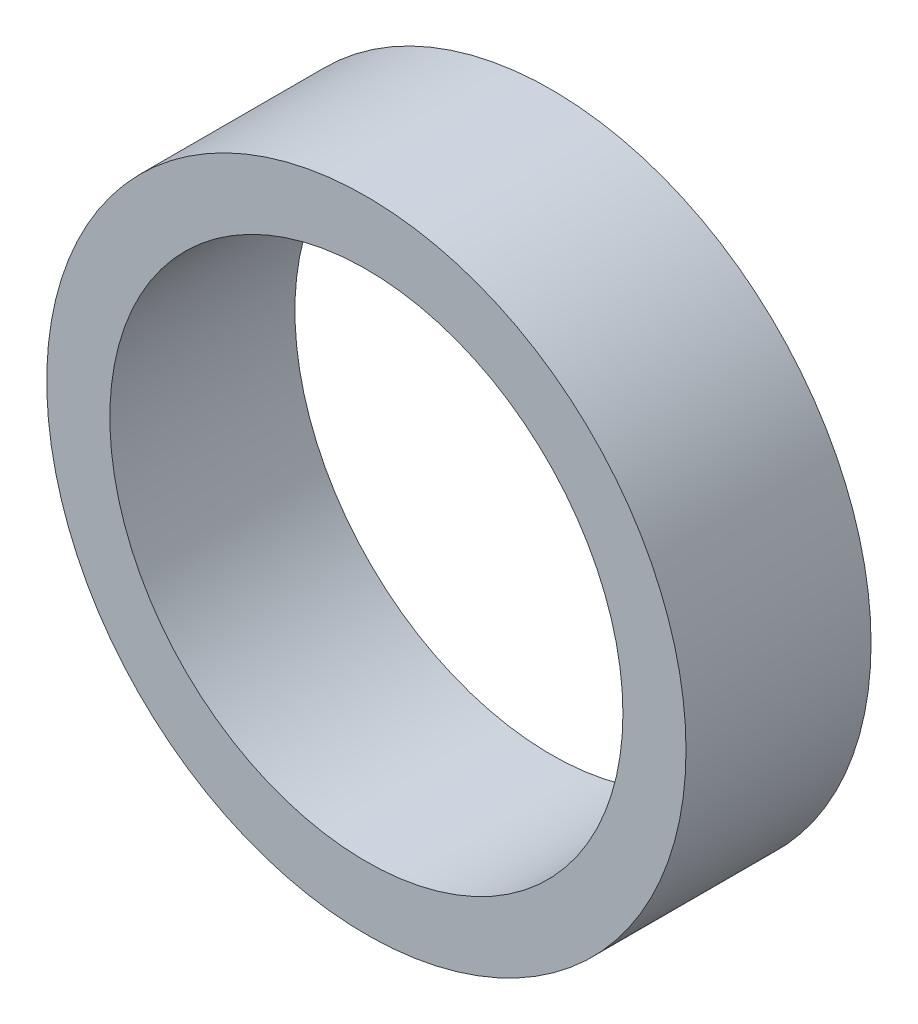
SolidWorks part; units mm, degrees
ref_plane "Front Plane" through (0, 0, 0) normal (0, 0, 1) x (1, 0, 0)
ref_plane "Top Plane" through (0, 0, 0) normal (0, 1, 0) x (1, 0, 0)
ref_plane "Right Plane" through (0, 0, 0) normal (1, 0, 0) x (0, 0, -1)
sketch "Sketch1" plane through (0, 0, 0) normal (0, 0, 1) x (1, 0, 0)
  circle A0 centre (0, 0) radius 19
  circle A1 centre (0, 0) radius 15.25
extrude "Boss-Extrude1" add sketch "Sketch1" along normal blind 11
